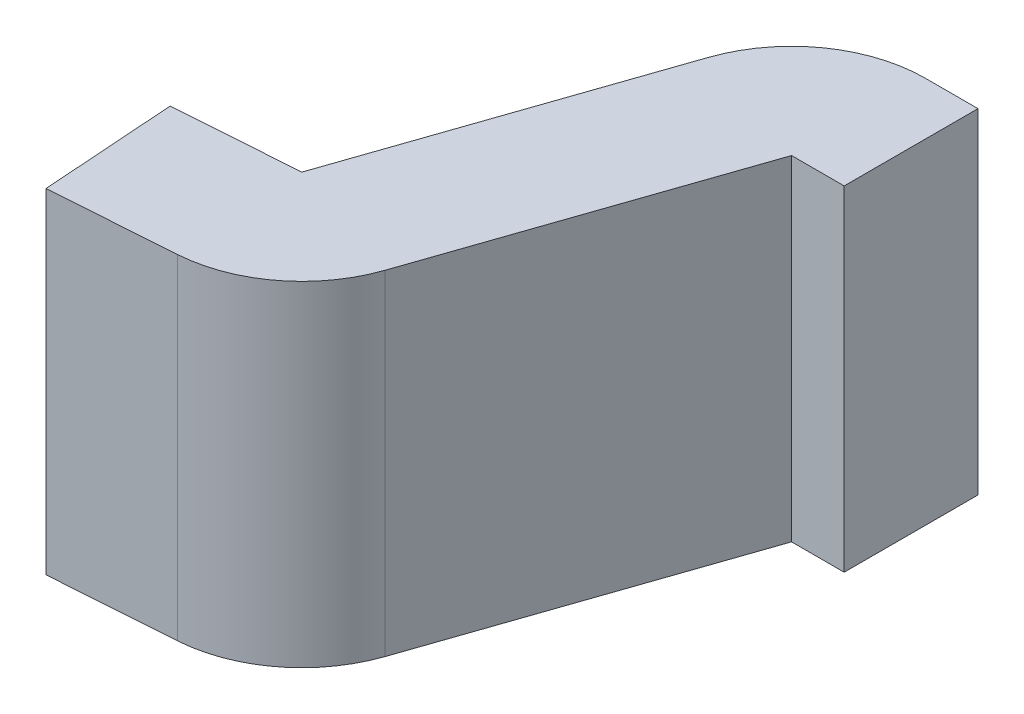
SolidWorks part; units mm, degrees
material "1060-H16"
ref_plane "Front Plane" through (0, 0, 0) normal (0, 0, 1) x (1, 0, 0)
ref_plane "Top Plane" through (0, 0, 0) normal (0, 1, 0) x (1, 0, 0)
ref_plane "Right Plane" through (0, 0, 0) normal (1, 0, 0) x (0, 0, -1)
sketch "Sketch2" plane through (0, 0, 0) normal (0, 1, 0) x (1, 0, 0)
  line L0 (0, 0) -> (0.6, 0) construction
  line L1 (0, 0) -> (0.1839, 0.0129) construction
  line L2 (0.2715, 0.0801) -> (0.4268, 0.5325) construction
  line L3 (0.5214, 0.6) -> (0.6, 0.6) construction
  line L4 (0.007, -0.0998) -> (0.1909, -0.0869)
  line L5 (0.3661, 0.0477) -> (0.5214, 0.5)
  line L6 (0.5214, 0.5) -> (0.6, 0.5)
  line L7 (-0.007, 0.0998) -> (0.1769, 0.1126)
  line L8 (0.1769, 0.1126) -> (0.3322, 0.5649)
  line L9 (0.5214, 0.7) -> (0.6, 0.7)
  line L10 (0.007, -0.0998) -> (-0.007, 0.0998)
  line L11 (0.6, 0.5) -> (0.6, 0.7)
  arc A0 (0.1839, 0.0129) -> (0.2715, 0.0801) centre (0.1769, 0.1126) ccw construction
  arc A1 (0.4268, 0.5325) -> (0.5214, 0.6) centre (0.5214, 0.5) cw construction
  arc A2 (0.1909, -0.0869) -> (0.3661, 0.0477) centre (0.1769, 0.1126) ccw
  arc A3 (0.5214, 0.5) -> (0.5214, 0.5) centre (0.5214, 0.5) cw
  arc A4 (0.1769, 0.1126) -> (0.1769, 0.1126) centre (0.1769, 0.1126) ccw
  arc A5 (0.3322, 0.5649) -> (0.5214, 0.7) centre (0.5214, 0.5) cw
  point P3 (0, 0)
  point P9 (0.25, 0.0175)
  point P12 (0.45, 0.6)
  dimension "D6" = 0.1
  dimension "D1" = 0.6
  dimension "D2" = 4
  dimension "D3" = 0.6
  dimension "D4" = 0.25
  dimension "D5" = 0.15
  dimension "D7" = 0.1
  dimension "D8" = 0.1
extrude "Boss-Extrude1" add sketch "Sketch2" along normal mid plane 0.5
